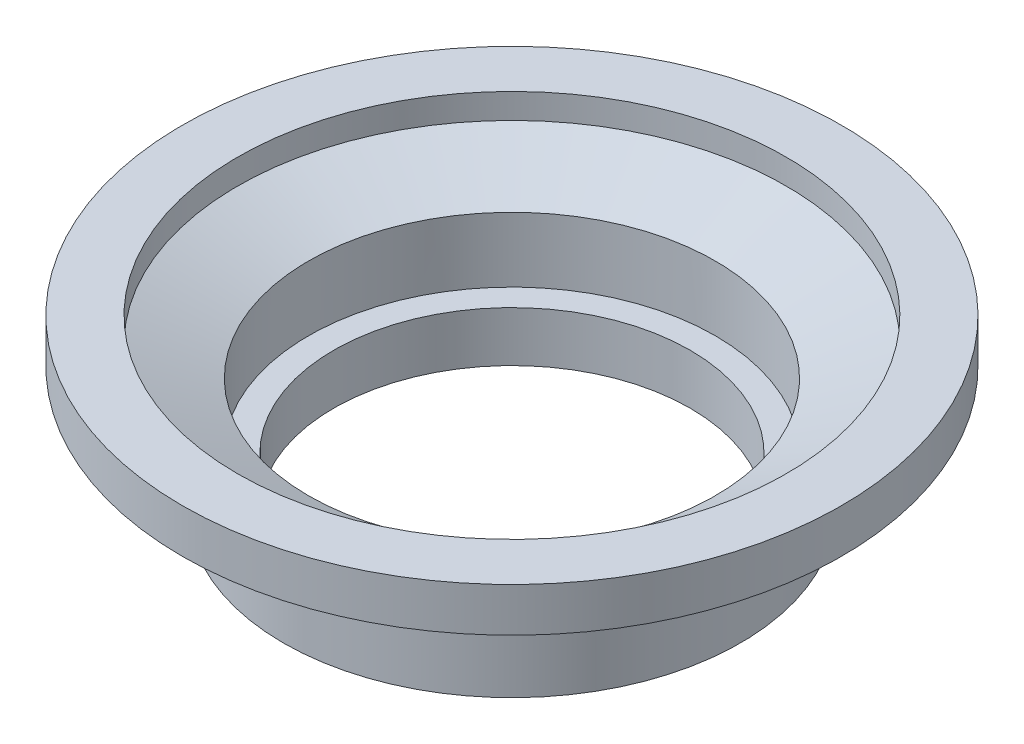
SolidWorks part; units mm, degrees
material "Titanium"
ref_plane "Front Plane" through (0, 0, 0) normal (0, 0, 1) x (1, 0, 0)
ref_plane "Top Plane" through (0, 0, 0) normal (0, 1, 0) x (1, 0, 0)
ref_plane "Right Plane" through (0, 0, 0) normal (1, 0, 0) x (0, 0, -1)
sketch "Sketch1" plane through (0, 0, 0) normal (0, 0, 1) x (1, 0, 0)
  line L0 (0, 0) -> (0, -6.5115) construction
  line L1 (4.6228, 0) -> (4.6228, 2.3038)
  line L2 (4.6228, 0) -> (4.1148, 0)
  line L3 (5.5499, 3.937) -> (6.6675, 3.937)
  line L4 (6.6675, 3.937) -> (6.6675, 3.048)
  line L5 (6.6675, 3.048) -> (4.6228, 2.3038)
  line L6 (4.1148, 0) -> (4.1148, 2.8346)
  line L7 (5.5499, 3.429) -> (5.5499, 1.4053) construction
  line L8 (5.5499, 3.937) -> (5.5499, 3.429)
  line L9 (5.5499, 3.429) -> (4.1148, 2.8346)
  line L10 (0, 0) -> (0, 5.3732) construction
  line L11 (4.1148, 2.8346) -> (0, 1.1302) construction
  line L12 (0, 1.1302) -> (-4.1148, 2.8346) construction
  dimension "D1" = 9.2456
  dimension "D2" = 13.335
  dimension "D3" = 3.937
  dimension "D4" = 0.889
  dimension "D5" = 20
  dimension "D6" = 8.2296
  dimension "D7" = 67.5
  dimension "D8" = 11.0998
  dimension "D9" = 0.508
  dimension "D10" = 0.508
  dimension "D11" = 1.1176
  dimension "D12" = 2.0447
  dimension "D13" = 135
revolve "Revolve1" add sketch "Sketch1" angle 360 about L0
sketch "Sketch3" plane through (0, 0, 0) normal (0, -1, 0) x (1, 0, 0)
  circle A0 centre (0, 0) radius 4.6228 construction
  circle A1 centre (0, 0) radius 4.1148 construction
  circle A2 centre (0, 0) radius 4.6228
  circle A3 centre (0, 0) radius 4.1148
extrude "Extrude2" cut sketch "Sketch3" against normal blind 0.508
sketch "Sketch4" plane through (0, 0.508, 0) normal (0, -1, 0) x (1, 0, 0)
  line L0 (-4.0833, 0.508) -> (4.0833, 0.508)
  line L1 (-4.0833, -0.508) -> (4.0833, -0.508)
  line L2 (0, 0.508) -> (0, -0.508) construction
  circle A0 centre (0, 0) radius 4.1148 construction
  arc A1 (4.0833, -0.508) -> (4.0833, 0.508) centre (0, 0) ccw
  arc A2 (-4.0833, 0.508) -> (-4.0833, -0.508) centre (0, 0) ccw
  point P8 (0, 0)
  dimension "D1" = 1.016
extrude "Extrude4" [suppressed] add sketch "Sketch4" against normal blind 1.016
fillet "Fillet1" [suppressed] radius 1.27
sketch "Sketch5" [suppressed] plane through (0, 0.508, 0) normal (0, -1, 0) x (1, 0, 0)
  line L0 (0, -0.508) -> (0, -4.1148) construction
  line L1 (-2.2207, -0.508) -> (2.2207, -0.508) construction
  line L2 (0, -4.6228) -> (0, -4.1148) construction
  arc A0 (-3.2121, -2.5718) -> (3.2121, -2.5717) centre (0, 0) ccw construction
  circle A1 centre (0, -2.3114) radius 1.8034 construction
  circle A2 centre (0, 0) radius 4.6228 construction
  circle A3 centre (0, 0) radius 4.6228 construction
  dimension "D1" = 3.6068
  dimension "D2" = 2.3114
sketch "Sketch6" plane through (0, 0.508, 0) normal (0, -1, 0) x (1, 0, 0)
  circle A0 centre (0, 0) radius 4.1148 construction
  circle A1 centre (0, 0) radius 4.1148
extrude "Extrude5" add sketch "Sketch6" against normal blind 1.016
sketch "Sketch7" plane through (0, 1.524, 0) normal (0, 1, 0) x (1, 0, 0)
  line L0 (0, 2.5908) -> (0, 4.1148) construction
  circle A0 centre (0, 2.5908) radius 1.524
  circle A1 centre (0, 0) radius 4.1148 construction
  circle A2 centre (0, 0) radius 4.1148 construction
  dimension "D1" = 3.048
extrude "Extrude6" [suppressed] cut sketch "Sketch7" against normal through all
pattern_circular "CirPattern1" [suppressed] count 4 over 360
sketch "Sketch8" plane through (0, 0.508, 0) normal (0, -1, 0) x (1, 0, 0)
  line L0 (0, 0) -> (8.8669, 0) construction
  line L1 (0, 0) -> (0, 6.6802) construction
sketch "Sketch9" [suppressed] plane through (0, 0, 0) normal (0, 0, 1) x (1, 0, 0)
  line L0 (0, 0.508) -> (0, -5.7586) construction
sketch "Sketch10" plane through (0, 0.508, 0) normal (0, -1, 0) x (1, 0, 0)
  line L0 (3.6068, 0) -> (4.6228, 0) construction
  circle A0 centre (0, 0) radius 3.6068
  circle A1 centre (0, 0) radius 4.6228 construction
  dimension "D2" = 7.2136
  dimension "D1" = 1.016
extrude "Extrude7" cut sketch "Sketch10" against normal through all
sketch "Sketch12" plane through (0, 1.524, 0) normal (0, 1, 0) x (1, 0, 0)
  line L0 (0, 0) -> (0, -4.1148) construction
  line L1 (0, 0) -> (0, -6.6802) construction
  circle A0 centre (0, 0) radius 4.1148 construction
  circle A1 centre (0, -2.286) radius 1.8288
  dimension "D1" = 3.6576
extrude "3 Hole design Extrude8" [suppressed] cut sketch "Sketch12" against normal through all
pattern_circular "CirPattern2" [suppressed] count 3 over 360
sketch "Sketch14" plane through (0, 1.524, 0) normal (0, 1, 0) x (1, 0, 0)
  line L0 (0, 0) -> (0, -6.6802) construction
  circle A0 centre (0, -0.9398) radius 3.175
  circle A1 centre (0, 0) radius 4.1148 construction
  circle A2 centre (0, 0) radius 4.1148 construction
  dimension "D1" = 6.35
extrude "Notch 4 Vent Hole Extrude8" [suppressed] cut sketch "Sketch14" against normal through all
